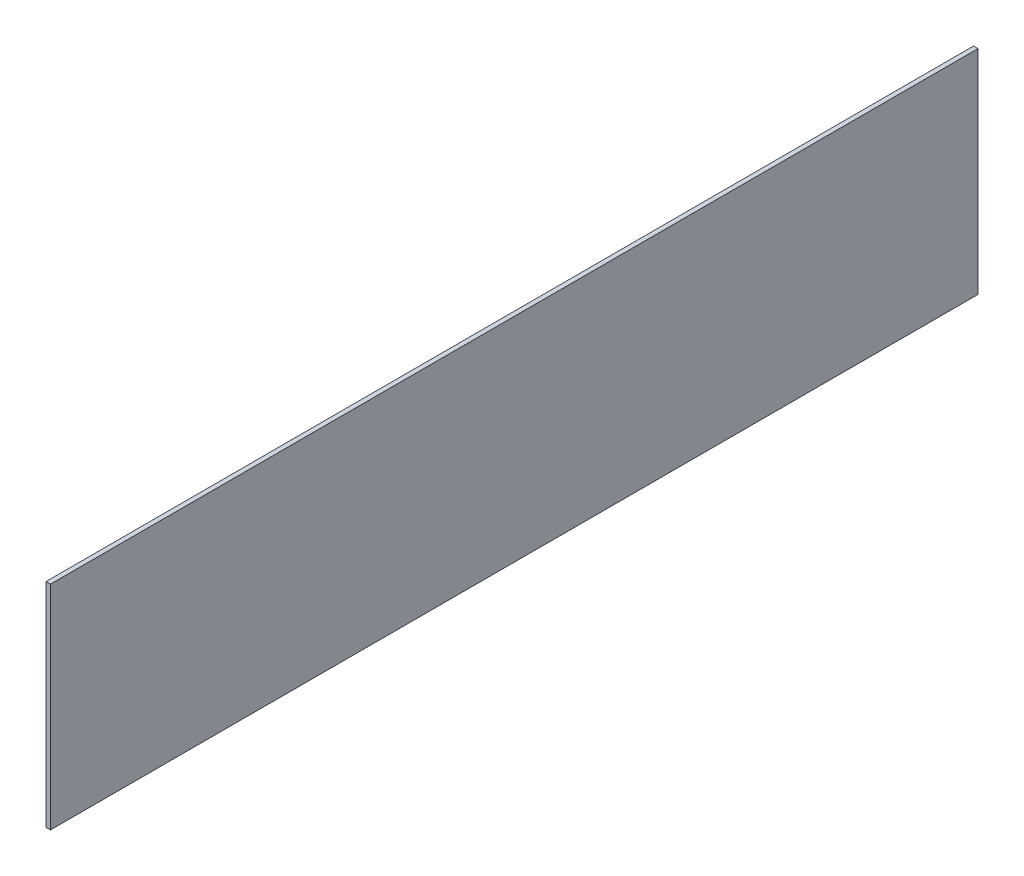
SolidWorks part; units mm, degrees
ref_plane "Front Plane" through (0, 0, 0) normal (0, 0, 1) x (1, 0, 0)
ref_plane "Top Plane" through (0, 0, 0) normal (0, 1, 0) x (1, 0, 0)
ref_plane "Right Plane" through (0, 0, 0) normal (1, 0, 0) x (0, 0, -1)
sketch "Sketch1" plane through (0, 0, 0) normal (1, 0, 0) x (0, 0, -1)
  line L0 (-311.5, 68.5) -> (-311.5, -71.5)
  line L1 (-311.5, -71.5) -> (308.5, -71.5)
  line L2 (308.5, -71.5) -> (311.5, -71.5)
  line L3 (311.5, -71.5) -> (311.5, 68.5)
  line L4 (311.5, 68.5) -> (311.5, 71.5)
  line L5 (311.5, 71.5) -> (-311.5, 71.5)
  line L6 (-311.5, 71.5) -> (-311.5, 68.5)
extrude "Boss-Extrude1" add sketch "Sketch1" along normal blind 3
